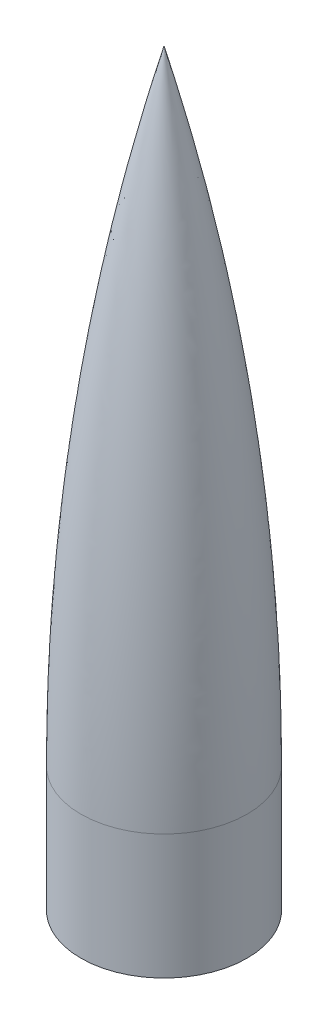
SolidWorks part; units mm, degrees
ref_plane "Front Plane" through (0, 0, 0) normal (0, 0, 1) x (1, 0, 0)
ref_plane "Top Plane" through (0, 0, 0) normal (0, 1, 0) x (1, 0, 0)
ref_plane "Right Plane" through (0, 0, 0) normal (1, 0, 0) x (0, 0, -1)
sketch "Sketch1" plane through (0, 0, 0) normal (0, 0, 1) x (1, 0, 0)
  line L0 (0, 0) -> (0, 95.6511) construction
  line L3 (50.8, 0) -> (50.8, 76.2)
  line L4 (49.53, 0) -> (49.53, 76.2)
  line L5 (50.8, 0) -> (49.53, 0)
  line L6 (0, 457.2) -> (0, 452.3237)
  arc A1 (50.8, 76.2) -> (0, 457.2) centre (-1403.35, 76.2) ccw
  arc A2 (49.53, 76.2) -> (0, 452.3237) centre (-1403.35, 76.2) ccw
  arc A3 (49.53, 76.2) -> (-1.2256, 456.8672) centre (-1403.35, 76.2) ccw construction
  dimension "D1" = 457.2
  dimension "D2" = 76.2
  dimension "D3" = 101.6
  dimension "D4" = 1.27
revolve "Revolve1" add sketch "Sketch1" angle 360 about L0
